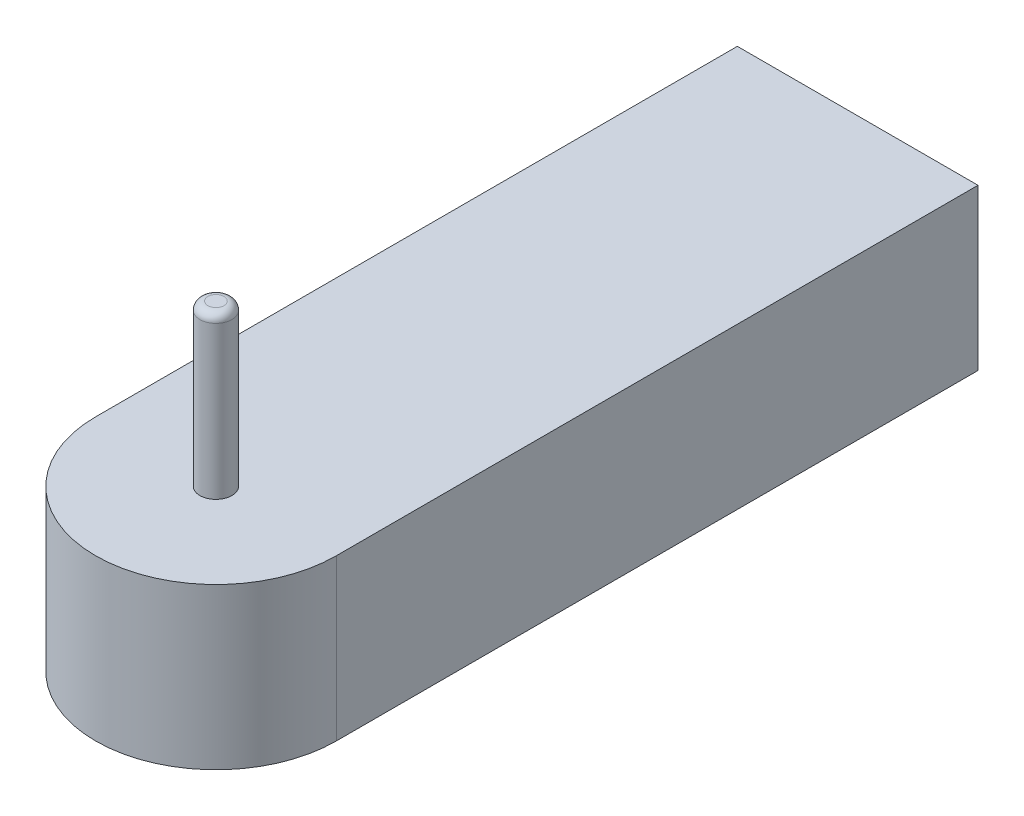
SolidWorks part; units mm, degrees
ref_plane "前视基准面" through (0, 0, 0) normal (0, 0, 1) x (1, 0, 0)
ref_plane "上视基准面" through (0, 0, 0) normal (0, 1, 0) x (1, 0, 0)
ref_plane "右视基准面" through (0, 0, 0) normal (1, 0, 0) x (0, 0, -1)
sketch "草图1" plane through (0, 0, 0) normal (0, 1, 0) x (1, 0, 0)
  line L1 (0, 0) -> (150, 0)
  line L2 (0, 0) -> (0, -400)
  line L3 (0, -400) -> (150, -400) construction
  line L4 (150, 0) -> (150, -400)
  arc A0 (0, -400) -> (150, -400) centre (75, -400) ccw
  dimension "D1" = 150
  dimension "D2" = 400
extrude "凸台-拉伸1" add sketch "草图1" along normal blind 100
sketch "草图2" plane through (0, 100, 0) normal (0, 1, 0) x (1, 0, 0)
  circle A0 centre (75, -400) radius 10
  dimension "D1" = 20
extrude "凸台-拉伸2" add sketch "草图2" along normal blind 100
fillet "圆角1" radius 5 1 edges at (75, 200, 410)
